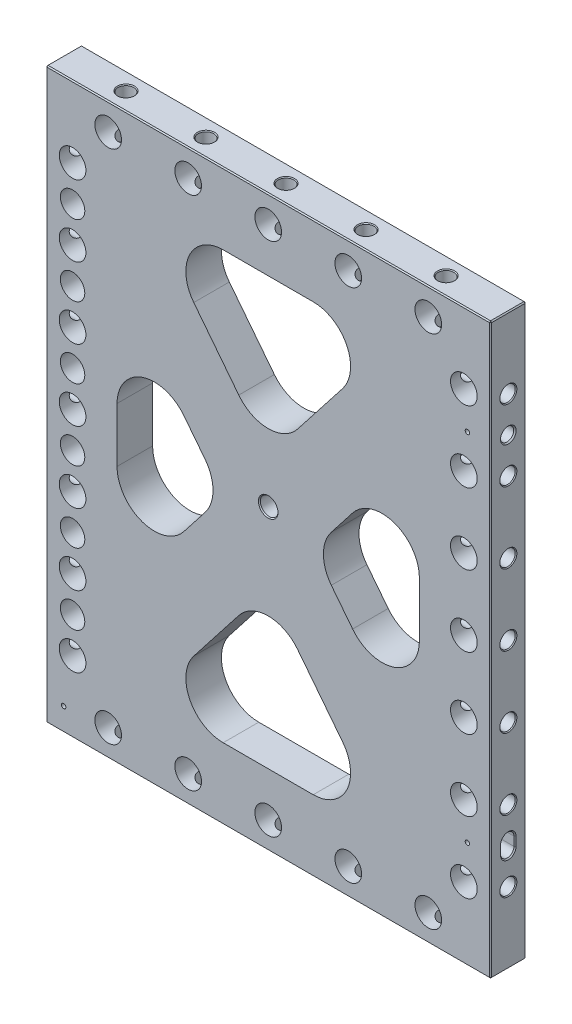
SolidWorks part; units mm, degrees
material "6061-T6 Al"
ref_plane "Front Plane" through (0, 0, 0) normal (0, 0, 1) x (1, 0, 0)
ref_plane "Top Plane" through (0, 0, 0) normal (0, 1, 0) x (1, 0, 0)
ref_plane "Right Plane" through (0, 0, 0) normal (1, 0, 0) x (0, 0, -1)
sketch "Sketch2" plane through (0, 0, 0) normal (0, 0, 1) x (1, 0, 0)
  line L0 (-158.75, -203.2) -> (158.75, 203.2) construction
  line L1 (-158.75, 203.2) -> (158.75, 203.2)
  line L2 (-158.75, 203.2) -> (-158.75, -203.2)
  line L3 (-158.75, -203.2) -> (158.75, -203.2)
  line L4 (158.75, 203.2) -> (158.75, -203.2)
  point P4 (0, 0)
  dimension "D1" = 317.5
  dimension "D2" = 406.4
extrude "Extrude1" add sketch "Sketch2" along normal mid plane 25.4
sketch "Sketch8" plane through (0, 0, 12.7) normal (0, 0, 1) x (1, 0, 0)
  line L0 (-158.75, 203.2) -> (158.75, -203.2) construction
  line L1 (158.75, 203.2) -> (-158.75, -203.2) construction
  line L2 (-107.95, 96.9184) -> (-32.2325, 0)
  line L3 (-32.2325, 0) -> (-107.95, -96.9184)
  line L4 (-107.95, -96.9184) -> (-107.95, 96.9184)
  line L5 (-86.83, 152.4) -> (0, 41.2576)
  line L6 (0, 41.2576) -> (86.83, 152.4)
  line L7 (86.83, 152.4) -> (-86.83, 152.4)
  line L8 (107.95, 96.9184) -> (107.95, -96.9184)
  line L9 (107.95, -96.9184) -> (32.2325, 0)
  line L10 (32.2325, 0) -> (107.95, 96.9184)
  line L11 (0, -41.2576) -> (-86.83, -152.4)
  line L12 (-86.83, -152.4) -> (86.83, -152.4)
  line L13 (86.83, -152.4) -> (0, -41.2576)
  line L14 (0, -41.2576) -> (-32.2325, 0) construction
  line L15 (-32.2325, 0) -> (0, 41.2576) construction
  line L16 (0, 41.2576) -> (0, 0) construction
  line L17 (0, 0) -> (0, -41.2576) construction
  line L18 (32.2325, 0) -> (0, 0) construction
  line L19 (0, 0) -> (-32.2325, 0) construction
  line L20 (-158.75, 203.2) -> (-158.75, -203.2) construction
  line L21 (158.75, 203.2) -> (-158.75, 203.2) construction
  point P19 (-16.1163, 20.6288)
  point P23 (-16.1163, -20.6288)
  point P24 (-158.75, 0)
  dimension "D1" = 50.8
  dimension "D2" = 50.8
  dimension "D3" = 50.8
extrude "Triangles -- Cut-Extrude2" cut sketch "Sketch8" against normal through all
fillet "Triangles -- Fillet1" radius 26.67 12 edges at (-107.95, -96.9184, 0) (-32.2325, 0, 0) (-86.83, -152.4, 0) (86.83, -152.4, 0) (0, -41.2576, 0) (32.2325, 0, 0) (107.95, -96.9184, 0) (107.95, 96.9184, 0) (86.83, 152.4, 0) (-86.83, 152.4, 0) (0, 41.2576, 0) (-107.95, 96.9184, 0)
hole_wizard "3/4 (0.75) Diameter Hole2" positions "Sketch4" profile "Sketch3" hole size "3/4" standard "Ansi Inch" end condition through all
sketch "Sketch4" plane through (0, 0, 12.7) normal (0, 0, 1) x (1, 0, 0)
  line L3 (0, 0) -> (-139.7, 0) construction
  line L6 (-158.75, 203.2) -> (-158.75, -203.2) construction
  point P0 (-139.7, 0)
  dimension "D1" = 19.05
sketch "Sketch3" plane through (-139.7, 0, 12.7) normal (1, 0, 0) x (0, -1, 0)
  line L0 (0, 0) -> (0, 25.4)
  line L1 (0, 25.4) -> (9.525, 25.4)
  line L2 (9.525, 25.4) -> (9.525, 0)
  line L5 (9.525, 0) -> (0, 0)
  line L11 (0, -6.35) -> (0, 107.95) construction
  dimension "Thru Hole Dia." = 19.05
  dimension "Thru Hole Depth" = 25.4
hole_wizard "7/16 (0.4375) Diameter Hole1" positions "Sketch6" profile "Sketch5" hole size "7/16" standard "Ansi Inch"
sketch "Sketch6" plane through (-158.75, 0, 0) normal (-1, 0, 0) x (0, 0, 1)
  point P0 (0, 0)
sketch "Sketch5" plane through (-158.75, 0, 0) normal (0, 1, 0) x (0, 0, 1)
  line L0 (0, 0) -> (0, 38.2635)
  line L1 (0, 38.2635) -> (5.5562, 34.925)
  line L2 (5.5562, 34.925) -> (5.5562, 0.6209)
  line L3 (5.5562, 0.6209) -> (6.096, 0)
  line L5 (6.096, 0) -> (0, 0)
  line L6 (-5.5562, 0.6209) -> (-6.096, 0) construction
  line L10 (0, 38.2635) -> (-5.5563, 34.925) construction
  line L11 (0, -6.35) -> (0, 107.95) construction
  dimension "Hole Dia." = 11.1125
  dimension "Hole Depth" = 34.925
  dimension "Near C'Sink Dia." = 12.192
  dimension "Near C'Sink Angle" = 82
  dimension "Drill Angle" = 118
pattern_linear "LPattern3" count 4 spacing 50.8 along (0, 1, 0) count 4 spacing 50.8 along (0, -1, 0) of "7/16 (0.4375) Diameter Hole1", "3/4 (0.75) Diameter Hole2"
mirror "Mirror1" about plane through (0, 0, 0) normal (1, 0, 0) of "3/4 (0.75) Diameter Hole2", "7/16 (0.4375) Diameter Hole1", "LPattern3"
hole_wizard "3/4 (0.75) Diameter Hole1" positions "Sketch11" profile "Sketch10" hole size "3/4" standard "Ansi Inch" end condition through all
sketch "Sketch11" plane through (0, 0, 12.7) normal (0, 0, 1) x (1, 0, 0)
  line L0 (0, 0) -> (0, -184.15) construction
  line L2 (-158.75, -203.2) -> (158.75, -203.2) construction
  point P0 (0, -184.15)
  dimension "D1" = 19.05
sketch "Sketch10" plane through (0, -184.15, 12.7) normal (1, 0, 0) x (0, -1, 0)
  line L0 (0, 0) -> (0, 25.4)
  line L1 (0, 25.4) -> (9.525, 25.4)
  line L2 (9.525, 25.4) -> (9.525, 0)
  line L5 (9.525, 0) -> (0, 0)
  line L11 (0, -6.35) -> (0, 107.95) construction
  dimension "Thru Hole Dia." = 19.05
  dimension "Thru Hole Depth" = 25.4
hole_wizard "7/16 (0.4375) Diameter Hole2" positions "Sketch13" profile "Sketch12" hole size "7/16" standard "Ansi Inch"
sketch "Sketch13" plane through (0, -203.2, 0) normal (0, -1, 0) x (1, 0, 0)
  point P0 (0, 0)
sketch "Sketch12" plane through (0, -203.2, 0) normal (1, 0, 0) x (0, 0, -1)
  line L0 (0, 0) -> (0, 38.2635)
  line L1 (0, 38.2635) -> (5.5562, 34.925)
  line L2 (5.5562, 34.925) -> (5.5562, 0.6209)
  line L3 (5.5562, 0.6209) -> (6.096, 0)
  line L5 (6.096, 0) -> (0, 0)
  line L6 (-5.5562, 0.6209) -> (-6.096, 0) construction
  line L10 (0, 38.2635) -> (-5.5563, 34.925) construction
  line L11 (0, -6.35) -> (0, 107.95) construction
  dimension "Hole Dia." = 11.1125
  dimension "Hole Depth" = 34.925
  dimension "Near C'Sink Dia." = 12.192
  dimension "Near C'Sink Angle" = 82
  dimension "Drill Angle" = 118
pattern_linear "LPattern4" count 3 spacing 57.15 along (1, 0, 0) count 3 spacing 57.15 along (-1, 0, 0) of "7/16 (0.4375) Diameter Hole2", "3/4 (0.75) Diameter Hole1"
mirror "Mirror2" about plane through (0, 0, 0) normal (0, 1, 0) of "3/4 (0.75) Diameter Hole1", "7/16 (0.4375) Diameter Hole2", "LPattern4"
hole_wizard "CBORE for 3/8 Socket Head Cap Screw1" positions "Sketch18" profile "Sketch17" counterbore size "3/8" standard "Ansi Inch" end condition through all
sketch "Sketch18" plane through (0, 0, 12.7) normal (0, 0, 1) x (1, 0, 0)
  line L0 (-139.7, 0) -> (-139.7, 50.8) construction
  line L1 (-139.7, 50.8) -> (-139.7, 101.6) construction
  line L2 (-139.7, 101.6) -> (-139.7, 152.4) construction
  line L5 (-139.7, 0) -> (-139.7, -50.8) construction
  line L6 (-139.7, -50.8) -> (-139.7, -101.6) construction
  line L7 (-139.7, -101.6) -> (-139.7, -152.4) construction
  point P0 (-139.7, 127)
  point P58 (-139.7, 76.2)
  point P60 (-139.7, 25.4)
  point P62 (-139.7, -25.4)
  point P64 (-139.7, -76.2)
  point P66 (-139.7, -127)
sketch "Sketch17" plane through (-139.7, 127, 12.7) normal (1, 0, 0) x (0, -1, 0)
  line L0 (0, 0) -> (0, 25.4)
  line L1 (5.1587, 24.614) -> (5.842, 25.4)
  line L2 (5.1587, 24.614) -> (5.1587, 12.7)
  line L3 (5.1587, 12.7) -> (8.7312, 12.7)
  line L4 (8.7312, 12.7) -> (8.7312, 0)
  line L5 (8.7312, 0) -> (0, 0)
  line L11 (0, -6.35) -> (0, 107.95) construction
  line L12 (5.842, 25.4) -> (0, 25.4)
  line L13 (-5.1587, 24.614) -> (-5.842, 25.4) construction
  dimension "Thru Hole Dia." = 10.3175
  dimension "Thru Hole Depth" = 25.4
  dimension "C'Bore Dia." = 17.4625
  dimension "C'Bore Depth" = 12.7
  dimension "Far C'Sink Dia." = 11.684
  dimension "Far C'Sink Angle" = 82
hole_wizard "3/8 (0.375) Pin + Lead-In Hole1" positions "Sketch21" profile "Sketch20" counterbore size "3/8" standard "Ansi Inch"
sketch "Sketch21" plane through (0, -203.2, 0) normal (0, -1, 0) x (1, 0, 0)
  line L0 (-158.75, 0) -> (-146.05, 0) construction
  line L1 (-158.75, 12.7) -> (-158.75, -12.7) construction
  point P0 (-146.05, 0)
  dimension "D1" = 12.7
sketch "Sketch20" plane through (-146.05, -203.2, 0) normal (1, 0, 0) x (0, 0, -1)
  line L0 (0, 0) -> (0, 21.9116)
  line L1 (0, 21.9116) -> (4.7625, 19.05)
  line L2 (4.7625, 19.05) -> (4.7625, 3.175)
  line L3 (4.7625, 3.175) -> (4.7879, 3.175)
  line L5 (4.7879, 3.175) -> (4.7879, 0.6282)
  line L6 (4.7879, 0.6282) -> (5.334, 0)
  line L7 (5.334, 0) -> (0, 0)
  line L8 (-4.7879, 0.6282) -> (-5.334, 0) construction
  line L10 (0, 21.9116) -> (-4.7625, 19.05) construction
  line L11 (0, -6.35) -> (0, 107.95) construction
  dimension "Hole Dia." = 9.525
  dimension "Hole Depth" = 19.05
  dimension "C'Bore Dia." = 9.5758
  dimension "C'Bore Depth" = 3.175
  dimension "Near C'Sink Dia." = 10.668
  dimension "Near C'Sink Angle" = 82
  dimension "Drill Angle" = 118
hole_wizard "3/8 (0.376) Pin Locate1" positions "Sketch23" profile "Sketch22" hole size "3/8" standard "Ansi Inch"
sketch "Sketch23" plane through (158.75, 0, 0) normal (1, 0, 0) x (0, 0, -1)
  line L0 (0, 152.4) -> (0, 101.6) construction
  point P0 (0, 127)
sketch "Sketch22" plane through (158.75, 127, 0) normal (0, 1, 0) x (0, 0, -1)
  line L0 (0, 0) -> (0, 21.9192)
  line L1 (0, 21.9192) -> (4.7752, 19.05)
  line L2 (4.7752, 19.05) -> (4.7752, 0.935)
  line L3 (4.7752, 0.935) -> (5.588, 0)
  line L5 (5.588, 0) -> (0, 0)
  line L6 (-4.7752, 0.935) -> (-5.588, 0) construction
  line L10 (0, 21.9192) -> (-4.7752, 19.05) construction
  line L11 (0, -6.35) -> (0, 107.95) construction
  dimension "Hole Dia." = 9.5504
  dimension "Hole Depth" = 19.05
  dimension "Near C'Sink Dia." = 11.176
  dimension "Near C'Sink Angle" = 82
  dimension "Drill Angle" = 118
sketch "Sketch24" plane through (158.75, 0, 0) normal (1, 0, 0) x (0, 0, -1)
  line L0 (0, -152.4) -> (0, -127) construction
  line L1 (0, -127) -> (0, -101.6) construction
  line L2 (0, -123.825) -> (0, -130.175) construction
  line L3 (-4.7752, -123.825) -> (-4.7752, -130.175)
  line L4 (4.7752, -123.825) -> (4.7752, -130.175)
  arc A0 (-4.7752, -123.825) -> (4.7752, -123.825) centre (0, -123.825) cw
  arc A1 (-4.7752, -130.175) -> (4.7752, -130.175) centre (0, -130.175) ccw
  point P8 (0, -127)
  dimension "D1" = 6.35
  dimension "D2" = 9.5504
  dimension "D3" = 4.7752
extrude "Slot Locate1" cut sketch "Sketch24" against normal blind 19.05
chamfer "Chamfer1" distance 0.762 angle 45 4 edges at (158.75, -127, -4.7752) (158.75, -119.0498, 0) (158.75, -134.9502, 0) (158.75, -127, 4.7752)
hole_wizard "1/8 (0.125) Diameter Hole1" positions "Sketch26" profile "Sketch25" hole size "1/8" standard "Ansi Inch"
sketch "Sketch26" plane through (0, 0, 12.7) normal (0, 0, 1) x (1, 0, 0)
  line L0 (139.7, 131.7752) -> (139.7, 122.2248) construction
  line L1 (139.7, -123.825) -> (139.7, -130.175) construction
  line L3 (139.7, 131.7752) -> (139.7, 122.2248)
  line L4 (139.7, -123.825) -> (139.7, -130.175)
  line L6 (-146.05, -184.15) -> (-146.05, -186.69) construction
  line L9 (139.7, -127) -> (142.24, -127) construction
  line L12 (139.7, 127) -> (142.24, 127) construction
  line L13 (-141.2875, -184.15) -> (-150.8125, -184.15) construction
  line L14 (-141.2875, -184.15) -> (-150.8125, -184.15)
  point P0 (-146.05, -186.69)
  point P24 (142.24, 127)
  point P26 (142.24, -127)
  dimension "D1" = 2.54
sketch "Sketch25" plane through (-146.05, -186.69, 12.7) normal (1, 0, 0) x (0, -1, 0)
  line L0 (0, 0) -> (0, 10.4789)
  line L1 (0, 10.4789) -> (1.5875, 9.525)
  line L2 (1.5875, 9.525) -> (1.5875, 0)
  line L5 (1.5875, 0) -> (0, 0)
  line L10 (0, 10.4789) -> (-1.5875, 9.525) construction
  line L11 (0, -6.35) -> (0, 107.95) construction
  dimension "Hole Dia." = 3.175
  dimension "Hole Depth" = 9.525
  dimension "Drill Angle" = 118
hole_wizard "1/2 (0.5) Diameter Hole1" positions "Sketch28" profile "Sketch27" hole size "1/2" standard "Ansi Inch" end condition through all
sketch "Sketch28" plane through (0, 0, -12.7) normal (0, 0, -1) x (-1, 0, 0)
  point P0 (0, 9.525)
  dimension "D1" = 9.525
sketch "Sketch27" plane through (0, 9.525, -12.7) normal (1, 0, 0) x (0, 1, 0)
  line L0 (0, 0) -> (0, 25.4)
  line L1 (0, 25.4) -> (6.985, 25.4)
  line L2 (6.35, 24.6695) -> (6.35, 0.7305)
  line L3 (6.35, 0.7305) -> (6.985, 0)
  line L5 (6.985, 0) -> (0, 0)
  line L6 (-6.35, 0.7305) -> (-6.985, 0) construction
  line L7 (6.985, 25.4) -> (6.35, 24.6695)
  line L8 (-6.985, 25.4) -> (-6.35, 24.6695) construction
  line L11 (0, -6.35) -> (0, 107.95) construction
  dimension "Thru Hole Dia." = 12.7
  dimension "Thru Hole Depth" = 25.4
  dimension "Near C'Sink Dia." = 13.97
  dimension "Near C'Sink Angle" = 82
  dimension "Far C'Sink Dia." = 13.97
  dimension "Far C'Sink Angle" = 82
chamfer "Chamfer2" distance 0.762 angle 45 12 edges at (0, -203.2, -12.7) (0, -203.2, 12.7) (-158.75, -203.2, 0) (158.75, -203.2, 0) (158.75, 0, -12.7) (158.75, 0, 12.7) (-158.75, 0, -12.7) (-158.75, 0, 12.7) (-158.75, 203.2, 0) (0, 203.2, -12.7) (158.75, 203.2, 0) (0, 203.2, 12.7)
